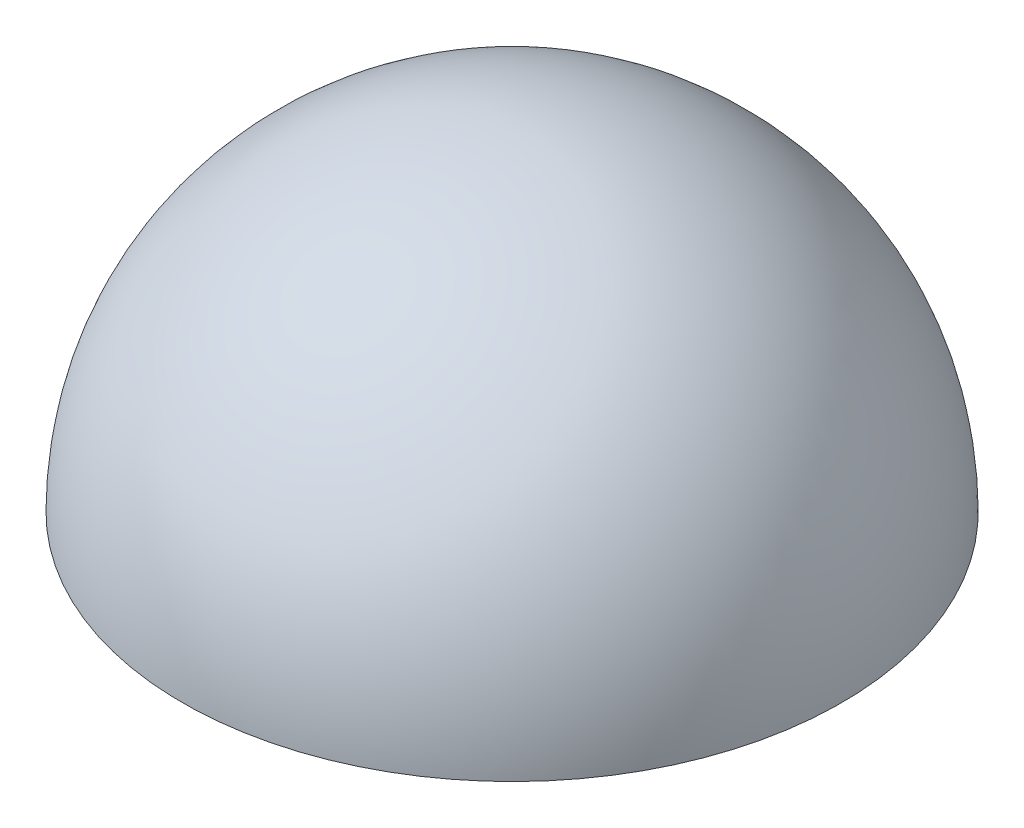
SolidWorks part; units mm, degrees
ref_plane "Front Plane" through (0, 0, 0) normal (0, 0, 1) x (1, 0, 0)
ref_plane "Top Plane" through (0, 0, 0) normal (0, 1, 0) x (1, 0, 0)
ref_plane "Right Plane" through (0, 0, 0) normal (1, 0, 0) x (0, 0, -1)
sketch "Sketch1" plane through (0, 0, 0) normal (1, 0, 0) x (0, 0, -1)
  line L0 (-7.0336, -54.9663) -> (-3.5336, -54.9663)
  line L1 (-7.0336, -54.9663) -> (-7.0336, -51.4663)
  arc A0 (-7.0336, -51.4663) -> (-3.5336, -54.9663) centre (-7.0336, -54.9663) cw
revolve "Revolve1" add sketch "Sketch1" angle 360 about L1
